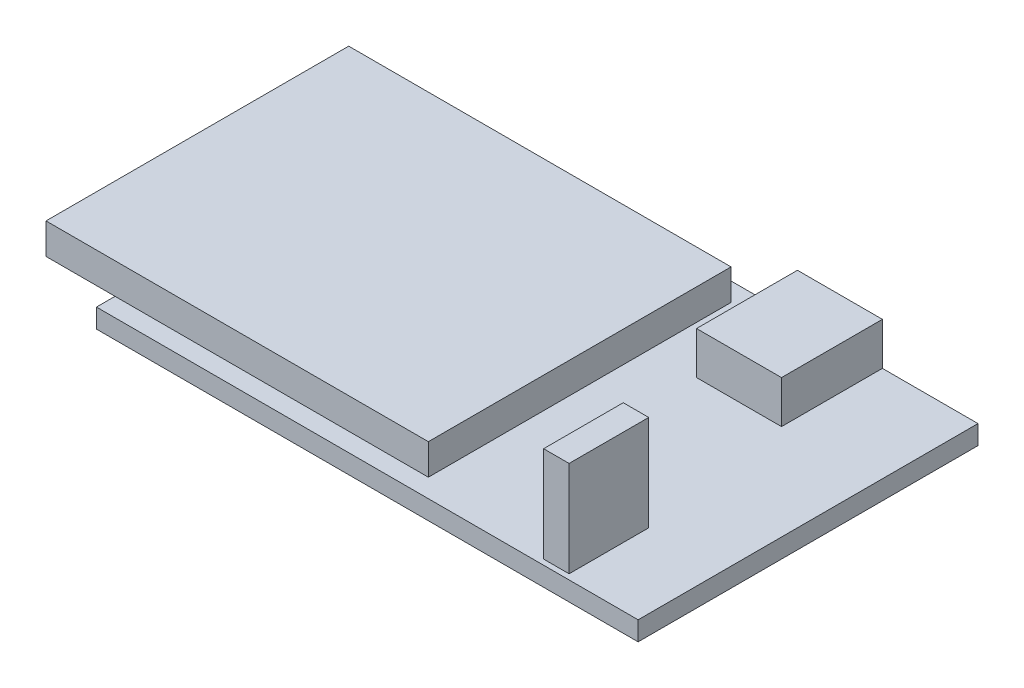
SolidWorks part; units mm, degrees
ref_plane "Front Plane" through (0, 0, 0) normal (0, 0, 1) x (1, 0, 0)
ref_plane "Top Plane" through (0, 0, 0) normal (0, 1, 0) x (1, 0, 0)
ref_plane "Right Plane" through (0, 0, 0) normal (1, 0, 0) x (0, 0, -1)
sketch "Sketch1" plane through (0, 0, 0) normal (0, 1, 0) x (1, 0, 0)
  line L1 (0, 0) -> (51, 0)
  line L2 (0, 0) -> (0, 32)
  line L3 (0, 32) -> (51, 32)
  line L4 (51, 0) -> (51, 32)
  dimension "D1" = 51
  dimension "D2" = 32
extrude "Boss-Extrude1" add sketch "Sketch1" along normal blind 1.8
sketch "Sketch2" plane through (0, 1.8, 0) normal (0, 1, 0) x (1, 0, 0)
  line L0 (0, 16) -> (51, 16) construction
  line L1 (29.5, 30.25) -> (-6.5, 30.25)
  line L2 (29.5, 30.25) -> (29.5, 1.75)
  line L3 (29.5, 1.75) -> (-6.5, 1.75)
  line L4 (-6.5, 30.25) -> (-6.5, 1.75)
  line L5 (0, 32) -> (0, 0) construction
  line L6 (51, 0) -> (51, 32) construction
  line L7 (29.5, 16) -> (-6.5, 16) construction
  dimension "D1" = 28.5
  dimension "D2" = 36
  dimension "D3" = 6.5
extrude "Boss-Extrude2" add sketch "Sketch2" along normal blind 2.9
sketch "Sketch3" plane through (0, 1.8, 0) normal (0, 1, 0) x (1, 0, 0)
  line L0 (51, 0) -> (51, 32) construction
  line L1 (41.6, 8) -> (44, 8)
  line L2 (41.6, 8) -> (41.6, 0.5)
  line L3 (41.6, 0.5) -> (44, 0.5)
  line L4 (44, 8) -> (44, 0.5)
  line L5 (0, 0) -> (51, 0) construction
  dimension "D1" = 2.4
  dimension "D2" = 7.5
  dimension "D3" = 7
  dimension "D4" = 0.5
extrude "Boss-Extrude3" add sketch "Sketch3" along normal blind 9
sketch "Sketch4" plane through (0, 1.8, 0) normal (0, 1, 0) x (1, 0, 0)
  line L0 (51, 32) -> (0, 32) construction
  line L1 (34, 32) -> (42, 32)
  line L2 (34, 32) -> (34, 22.5)
  line L3 (34, 22.5) -> (42, 22.5)
  line L4 (42, 32) -> (42, 22.5)
  line L5 (51, 0) -> (51, 32) construction
  dimension "D1" = 8
  dimension "D2" = 9.5
  dimension "D3" = 9
extrude "Boss-Extrude4" add sketch "Sketch4" along normal blind 4
ref_plane "Midplane" through (22.25, 0, 0) normal (1, 0, 0) x (0, 0, -1)
